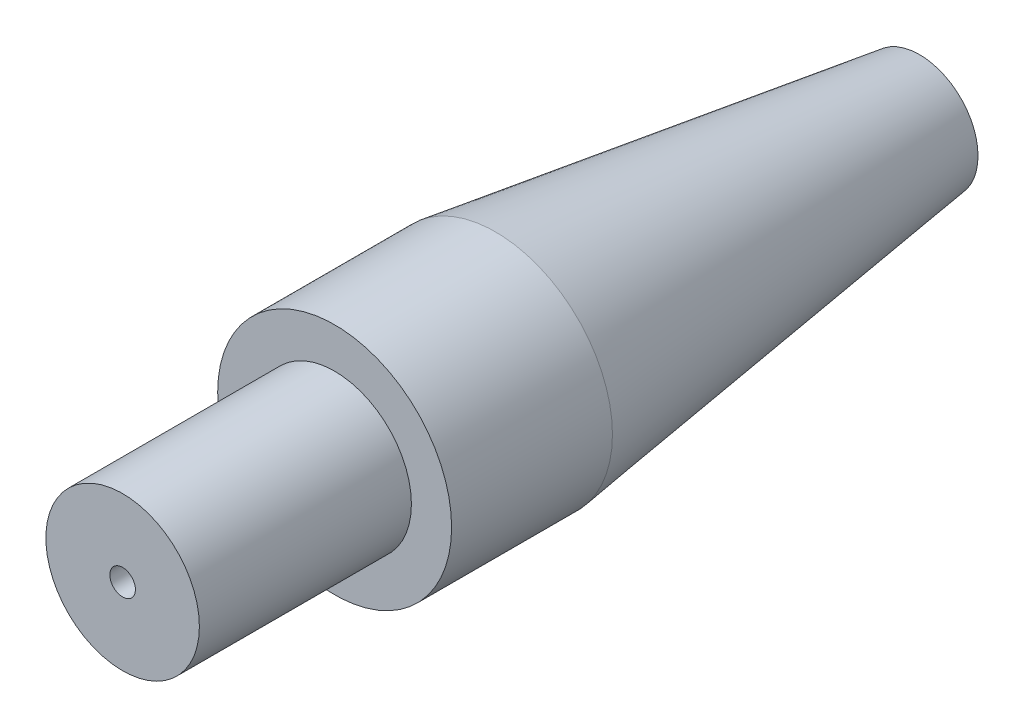
SolidWorks part; units mm, degrees
ref_plane "Front Plane" through (0, 0, 0) normal (0, 0, 1) x (1, 0, 0)
ref_plane "Top Plane" through (0, 0, 0) normal (0, 1, 0) x (1, 0, 0)
ref_plane "Right Plane" through (0, 0, 0) normal (1, 0, 0) x (0, 0, -1)
sketch "Sketch2" plane through (0, 0, 0) normal (0, 1, 0) x (1, 0, 0)
  line L0 (0, 0) -> (0, 20.32) construction
  line L1 (0.4445, 20.32) -> (0.4445, -7.366)
  line L2 (4.064, 0) -> (4.064, 5.588)
  line L3 (0.4445, 20.32) -> (2.032, 20.32)
  line L4 (2.032, 20.32) -> (4.064, 5.588)
  line L5 (4.064, 0) -> (2.667, 0)
  line L6 (2.667, 0) -> (2.667, -7.366)
  line L7 (2.667, -7.366) -> (0.4445, -7.366)
  point P9 (0, 0)
  point P11 (0, 0)
  point P13 (0.5359, -7.547)
  dimension "D1" = 20.32
  dimension "D2" = 4.064
  dimension "D3" = 0.4445
  dimension "D4" = 2.032
  dimension "D5" = 5.588
  dimension "D6" = 2.667
  dimension "D7" = 7.366
revolve "Revolve1" add sketch "Sketch2" angle 360 about L0
